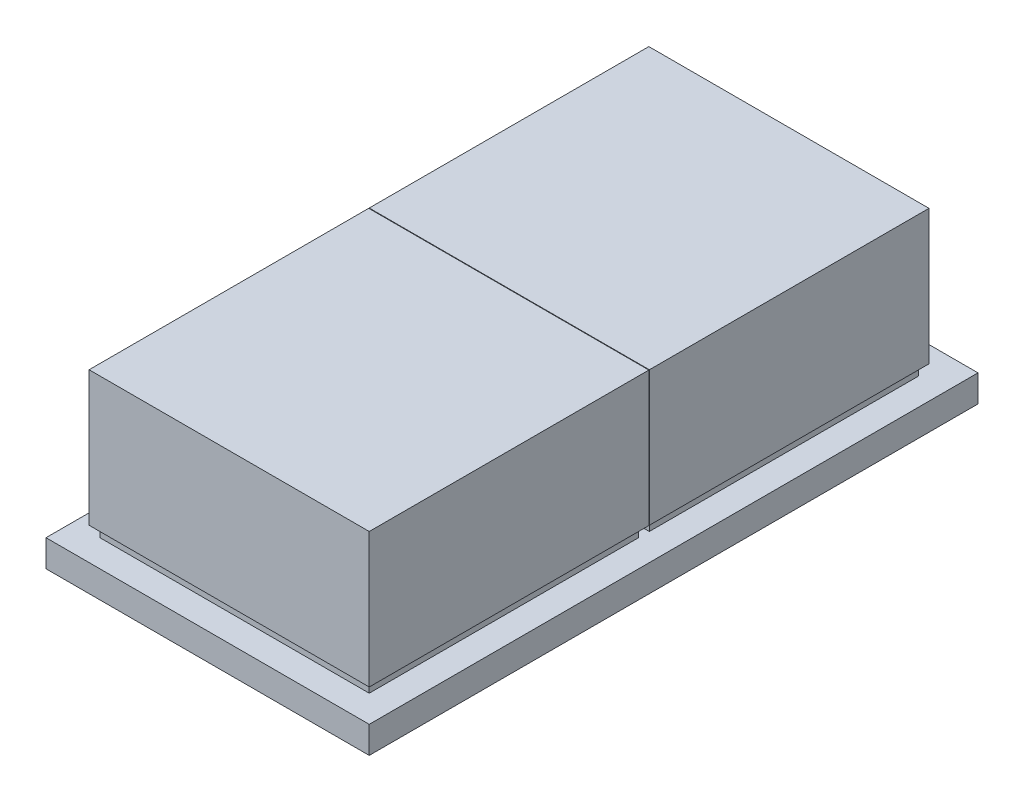
SolidWorks part; units mm, degrees
ref_plane "Front Plane" through (0, 0, 0) normal (0, 0, 1) x (1, 0, 0)
ref_plane "Top Plane" through (0, 0, 0) normal (0, 1, 0) x (1, 0, 0)
ref_plane "Right Plane" through (0, 0, 0) normal (1, 0, 0) x (0, 0, -1)
sketch "Sketch1" plane through (0, 0, 0) normal (0, 1, 0) x (1, 0, 0)
  line L1 (-30, -56.5) -> (30, -56.5)
  line L2 (-30, -56.5) -> (-30, 56.5)
  line L3 (-30, 56.5) -> (30, 56.5)
  line L4 (30, -56.5) -> (30, 56.5)
  line L5 (-30, -56.5) -> (30, 56.5) construction
  line L6 (-30, 56.5) -> (30, -56.5) construction
  point P0 (0, 0)
  dimension "D1" = 60
  dimension "D2" = 113
extrude "Boss-Extrude1" add sketch "Sketch1" along normal blind 5
sketch "Sketch2" plane through (0, 5, 0) normal (0, 1, 0) x (1, 0, 0)
  line L0 (0, 0) -> (0, -56.5) construction
  line L1 (-30, -56.5) -> (30, -56.5) construction
  line L3 (-25, -1.5) -> (25, -1.5)
  line L4 (-25, -1.5) -> (-25, -51.5)
  line L5 (-25, -51.5) -> (25, -51.5)
  line L6 (25, -1.5) -> (25, -51.5)
  line L7 (-25, -1.5) -> (25, -51.5) construction
  line L8 (-25, -51.5) -> (25, -1.5) construction
  point P5 (0, -26.5)
  dimension "D1" = 50
  dimension "D2" = 50
  dimension "D3" = 5
extrude "Boss-Extrude3" add sketch "Sketch2" along normal blind 2
pattern_linear "LPattern1" count 2 spacing 52 along (0, 0, -1) of "Boss-Extrude3"
sketch "Sketch3" plane through (0, 7, 0) normal (0, 1, 0) x (1, 0, 0)
  line L0 (0, 0) -> (0, -51.5) construction
  line L1 (-25, -51.5) -> (25, -51.5) construction
  line L3 (-26, -0.6) -> (26, -0.6)
  line L4 (-26, -0.6) -> (-26, -52.5)
  line L5 (-26, -52.5) -> (26, -52.5)
  line L6 (26, -0.6) -> (26, -52.5)
  line L7 (-26, -0.6) -> (26, -52.5) construction
  line L8 (-26, -52.5) -> (26, -0.6) construction
  line L9 (-30, -56.5) -> (30, -56.5) construction
  point P5 (0, -26.55)
  dimension "D1" = 52
  dimension "D2" = 51.9
  dimension "D3" = 4
extrude "Boss-Extrude8" add sketch "Sketch3" along normal blind 25
pattern_linear "LPattern5" count 2 spacing 52 along (0, 0, -1) of "Boss-Extrude8"
